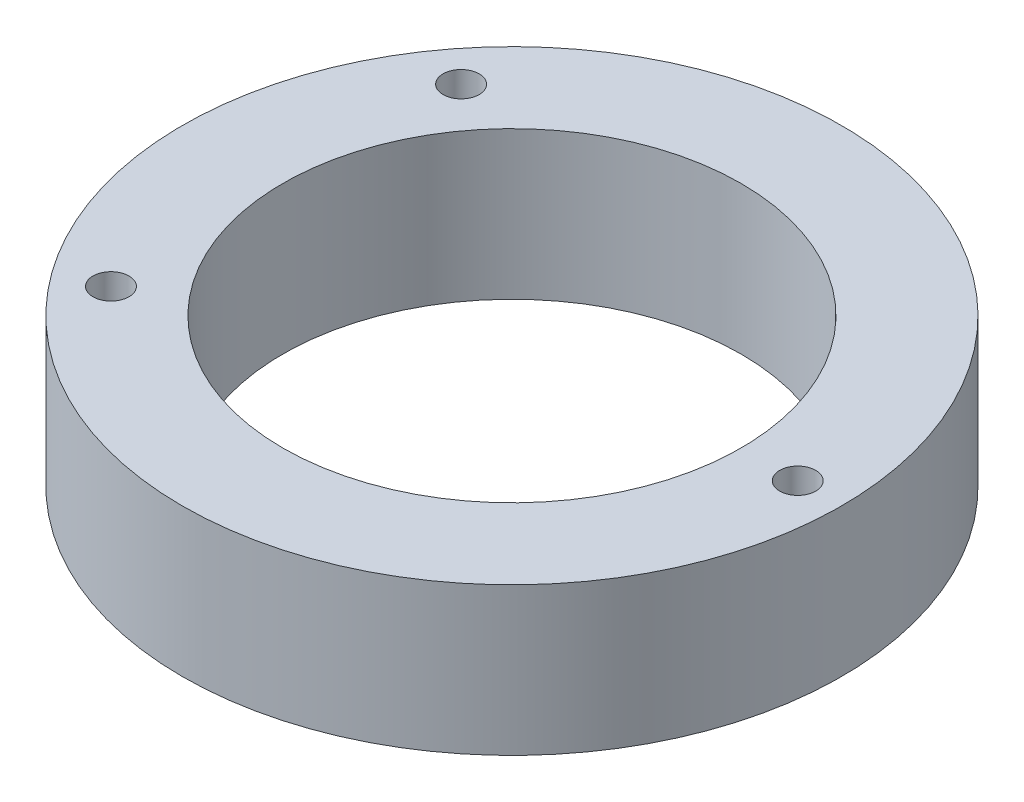
SolidWorks part; units mm, degrees
ref_plane "Płaszczyzna przednia" through (0, 0, 0) normal (0, 0, 1) x (1, 0, 0)
ref_plane "Płaszczyzna górna" through (0, 0, 0) normal (0, 1, 0) x (1, 0, 0)
ref_plane "Płaszczyzna prawa" through (0, 0, 0) normal (1, 0, 0) x (0, 0, -1)
sketch "Szkic1" plane through (0, 0, 0) normal (0, 1, 0) x (1, 0, 0)
  line L0 (-21.9327, 17.0005) -> (0, 0) construction
  line L1 (0, 0) -> (-21.9327, -17.0005) construction
  line L2 (0, 0) -> (27.75, 0) construction
  line L3 (-21.9327, 17.0005) -> (-21.9327, -17.0005) construction
  circle A0 centre (0, 0) radius 22.25
  circle A1 centre (0, 0) radius 32
  circle A2 centre (27.75, 0) radius 1.75
  circle A3 centre (-21.9327, -17.0005) radius 1.75
  circle A4 centre (-21.9327, 17.0005) radius 1.75
  dimension "D1" = 44.5
  dimension "D2" = 64
  dimension "D5" = 3.5
  dimension "D3" = 75.56
  dimension "D4" = 27.75
extrude "Dodanie-wyciągnięcie1" add sketch "Szkic1" along normal blind 14.35
